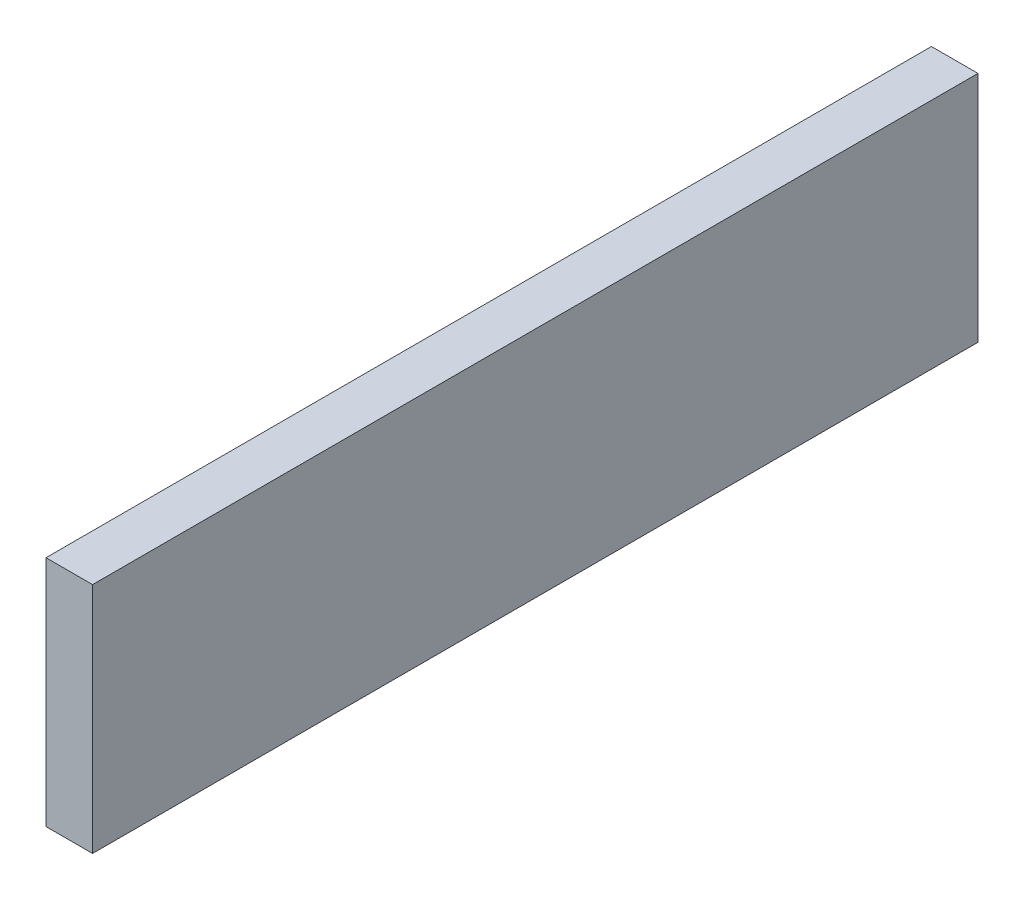
SolidWorks part; units mm, degrees
ref_plane "Plane1" through (0, 0, 0) normal (0, 0, 1) x (1, 0, 0)
ref_plane "Plane2" through (0, 0, 0) normal (0, 1, 0) x (1, 0, 0)
ref_plane "Plane3" through (0, 0, 0) normal (1, 0, 0) x (0, 0, -1)
sketch "Эскиз1" plane through (0, 0, 0) normal (0, 0, 1) x (1, 0, 0)
  line L0 (0, 0) -> (789, 0) construction
  line L1 (315.6, 0) -> (473.4, 0)
  line L2 (315.6, 0) -> (315.6, 789)
  line L3 (315.6, 789) -> (473.4, 789)
  line L4 (473.4, 0) -> (473.4, 789)
  line L5 (0, 789) -> (789, 789) construction
extrude "Вытянуть1" add sketch "Эскиз1" against normal blind 3000
